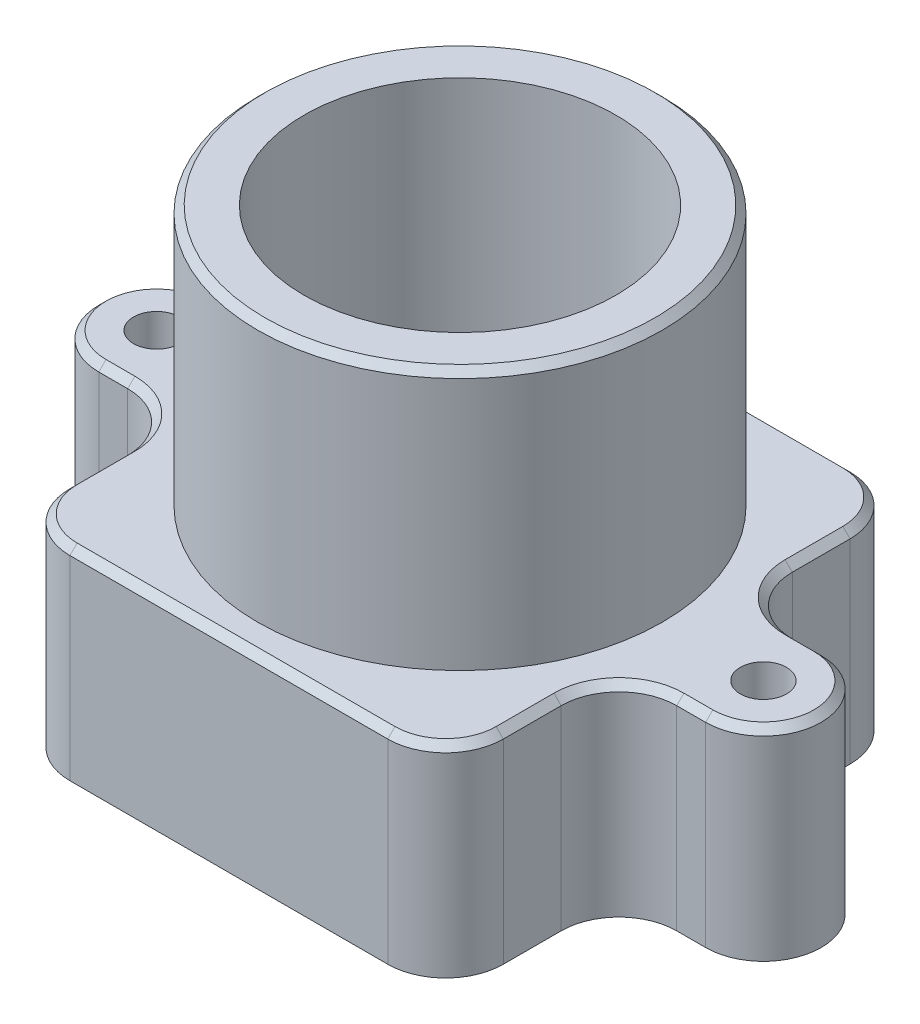
SolidWorks part; units mm, degrees
material "6061-T6 (SS)"
ref_plane "Front Plane" through (0, 0, 0) normal (0, 0, 1) x (1, 0, 0)
ref_plane "Top Plane" through (0, 0, 0) normal (0, 1, 0) x (1, 0, 0)
ref_plane "Right Plane" through (0, 0, 0) normal (1, 0, 0) x (0, 0, -1)
sketch "Sketch1" plane through (0, 0, 0) normal (0, 1, 0) x (1, 0, 0)
  line L0 (-10.5, 0) -> (10.5, 0) construction
  line L1 (-7.5, 8) -> (7.5, 8)
  line L2 (-7.5, 8) -> (-7.5, 2)
  line L3 (-7.5, -8) -> (7.5, -8)
  line L4 (7.5, 8) -> (7.5, 2)
  line L5 (-7.5, 8) -> (7.5, -8) construction
  line L6 (-7.5, -8) -> (7.5, 8) construction
  line L7 (-10.5, 2) -> (-7.5, 2)
  line L8 (-10.5, -2) -> (-7.5, -2)
  line L9 (10.5, 2) -> (7.5, 2)
  line L10 (10.5, -2) -> (7.5, -2)
  line L11 (-7.5, -2) -> (-7.5, -8)
  line L12 (7.5, -2) -> (7.5, -8)
  arc A0 (-10.5, 2) -> (-10.5, -2) centre (-10.5, 0) ccw
  arc A1 (10.5, -2) -> (10.5, 2) centre (10.5, 0) ccw
  point P0 (0, 0)
  dimension "D3" = 4
  dimension "D1" = 15
  dimension "D2" = 21
  dimension "D4" = 16
extrude "Boss-Extrude1" add sketch "Sketch1" along normal blind 7
fillet "Fillet1" radius 2 8 edges at (7.5, 3.5, -2) (7.5, 3.5, -8) (-7.5, 3.5, -8) (-7.5, 3.5, -2) (-7.5, 3.5, 2) (-7.5, 3.5, 8) (7.5, 3.5, 2) (7.5, 3.5, 8)
hole_wizard "M2x0.4 Tapped Hole1" positions "Sketch2" profile "Sketch3" tap size "M2x0.4" standard "ANSI Metric" end condition through all
sketch "Sketch2" plane through (0, 7, 0) normal (0, 1, 0) x (1, 0, 0)
  arc A0 (-10.5, 2) -> (-10.5, -2) centre (-10.5, 0) ccw construction
  arc A1 (10.5, -2) -> (10.5, 2) centre (10.5, 0) ccw construction
  point P0 (10.5, 0)
  point P2 (-10.5, 0)
sketch "Sketch3" plane through (10.5, 7, 0) normal (1, 0, 0) x (0, 0, 1)
  line L0 (0, 0) -> (0, 7)
  line L1 (0, 7) -> (0.8, 7)
  line L2 (0.8, 7) -> (0.8, 0)
  line L5 (0.8, 0) -> (0, 0)
  line L11 (0, -6.35) -> (0, 107.95) construction
  dimension "Thru Tap Drill Dia." = 1.6
  dimension "Thru Tap Drill Depth" = 7
cosmetic thread "Hole Thread1" parameters "D2"=2
cosmetic thread "Hole Thread2" parameters "D2"=2
chamfer "Chamfer1" distance 0.25 angle 45 20 edges at (0, 7, -8) (-6.9142, 7, -7.4142) (6.9142, 7, -7.4142) (-7.5, 7, -5) (7.5, 7, -5) (-8.0858, 7, -2.5858) (8.0858, 7, -2.5858) (-10, 7, -2) (10, 7, -2) (-12.5, 7, 0) (12.5, 7, 0) (-10, 7, 2) (10, 7, 2) (-8.0858, 7, 2.5858) (8.0858, 7, 2.5858) (-7.5, 7, 5) (7.5, 7, 5) (-6.9142, 7, 7.4142) (6.9142, 7, 7.4142) (0, 7, 8)
sketch "Sketch4" plane through (0, 7, 0) normal (0, 1, 0) x (1, 0, 0)
  circle A0 centre (0, 0) radius 7
  dimension "D1" = 14
extrude "Boss-Extrude2" add sketch "Sketch4" along normal blind 9
chamfer "Chamfer2" distance 0.25 angle 45 1 edges at (0, 16, 7)
hole_wizard "M12x1.25 Tapped Hole1" positions "Sketch5" profile "Sketch6" tap size "M12x1.25" standard "ANSI Metric" end condition through all
sketch "Sketch5" plane through (0, 16, 0) normal (0, 1, 0) x (1, 0, 0)
  point P0 (0, 0)
sketch "Sketch6" plane through (0, 16, 0) normal (1, 0, 0) x (0, 0, 1)
  line L0 (0, 0) -> (0, 16)
  line L1 (0, 16) -> (5.4, 16)
  line L2 (5.4, 16) -> (5.4, 0)
  line L5 (5.4, 0) -> (0, 0)
  line L11 (0, -6.35) -> (0, 107.95) construction
  dimension "Thru Tap Drill Dia." = 10.8
  dimension "Thru Tap Drill Depth" = 16
cosmetic thread "Hole Thread3" parameters "D2"=12
